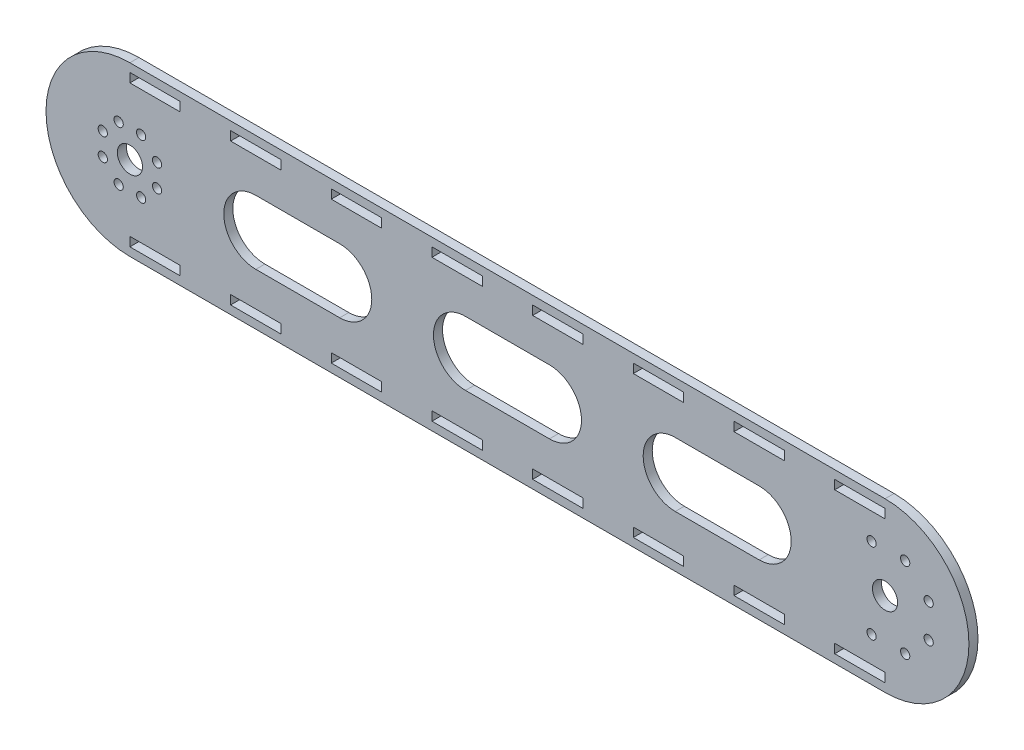
SolidWorks part; units mm, degrees
ref_plane "Front Plane" through (0, 0, 0) normal (0, 0, 1) x (1, 0, 0)
ref_plane "Top Plane" through (0, 0, 0) normal (0, 1, 0) x (1, 0, 0)
ref_plane "Right Plane" through (0, 0, 0) normal (1, 0, 0) x (0, 0, -1)
sketch "Sketch3" plane through (0, 0, 0) normal (0, 0, 1) x (1, 0, 0)
  line L0 (-20.9627, 0) -> (429.0373, 0) construction
  line L1 (-20.9627, 50) -> (429.0373, 50)
  line L2 (-20.9627, -50) -> (429.0373, -50)
  line L3 (179.0373, 0) -> (229.0373, 0) construction
  line L4 (179.0373, 19.0946) -> (229.0373, 19.0946)
  line L5 (179.0373, -19.0946) -> (229.0373, -19.0946)
  line L9 (-20.9627, 0) -> (-4.7949, 6.697)
  line L10 (-20.9627, 0) -> (-4.7949, 6.697) construction
  line L11 (-20.9627, 0) -> (-4.7949, -6.697) construction
  line L36 (-101.4371, 0) -> (436.7316, 0) construction
  line L64 (304.0053, 0) -> (354.0053, 0) construction
  line L65 (304.0053, 19.0946) -> (354.0053, 19.0946)
  line L66 (304.0053, -19.0946) -> (354.0053, -19.0946)
  line L67 (54.0693, 0) -> (104.0693, 0) construction
  line L68 (54.0693, 19.0946) -> (104.0693, 19.0946)
  line L69 (54.0693, -19.0946) -> (104.0693, -19.0946)
  line L99 (385.0007, 50) -> (385.0007, 44.46)
  arc A0 (-20.9627, 50) -> (-20.9627, -50) centre (-20.9627, 0) ccw
  arc A1 (429.0373, -50) -> (429.0373, 50) centre (429.0373, 0) ccw
  circle A2 centre (-20.9627, 0) radius 7.5
  circle A3 centre (429.0373, 0) radius 7.5
  arc A4 (179.0373, 19.0946) -> (179.0373, -19.0946) centre (179.0373, 0) ccw
  arc A5 (229.0373, -19.0946) -> (229.0373, 19.0946) centre (229.0373, 0) ccw
  circle A8 centre (-4.7949, 6.697) radius 2.75
  circle A9 centre (-4.7949, -6.697) radius 2.75
  circle A10 centre (-14.2658, -16.1679) radius 2.75
  circle A11 centre (-27.6597, -16.1679) radius 2.75
  circle A12 centre (-37.1306, -6.697) radius 2.75
  circle A13 centre (-37.1306, 6.697) radius 2.75
  circle A14 centre (-27.6597, 16.1679) radius 2.75
  circle A15 centre (-14.2658, 16.1679) radius 2.75
  circle A16 centre (455.0373, 10) radius 2.75
  circle A17 centre (441.0373, 24) radius 2.75
  circle A18 centre (421.0373, 24) radius 2.75
  circle A19 centre (455.0373, -10) radius 2.75
  circle A20 centre (441.0373, -24) radius 2.75
  circle A21 centre (421.0373, -24) radius 2.75
  arc A22 (304.0053, 19.0946) -> (304.0053, -19.0946) centre (304.0053, 0) ccw
  arc A23 (354.0053, -19.0946) -> (354.0053, 19.0946) centre (354.0053, 0) ccw
  arc A24 (54.0693, 19.0946) -> (54.0693, -19.0946) centre (54.0693, 0) ccw
  arc A25 (104.0693, -19.0946) -> (104.0693, 19.0946) centre (104.0693, 0) ccw
  point P3 (204.0373, 0)
  point P14 (204.0373, 0)
  point P59 (329.0053, 0)
  point P66 (79.0693, 0)
  dimension "D2" = 50
  dimension "D3" = 15
  dimension "D4" = 15
  dimension "D7" = 5.5
  dimension "D21" = 5.5
  dimension "D22" = 5.5
  dimension "D23" = 5.5
  dimension "D1" = 450
  dimension "D5" = 17.5
  dimension "D6" = 22.5
  dimension "D9" = 45
  dimension "D15" = 24
  dimension "D16" = 24
  dimension "D17" = 8
  dimension "D18" = 20
  dimension "D19" = 26
  dimension "D20" = 10
  dimension "D24" = 50
  dimension "D25" = 0
  dimension "D26" = 2
  dimension "D14" = 2
  dimension "D8" = 8
extrude "Boss-Extrude1" add sketch "Sketch3" along normal blind 5.4
sketch "Sketch4" plane through (0, 0, 5.4) normal (0, 0, 1) x (1, 0, 0)
  line L0 (-70.9627, 0) -> (479.0373, 0) construction
  line L1 (-20.9627, 50) -> (429.0373, 50) construction
  line L2 (-20.9627, 45) -> (9.0373, 45)
  line L3 (-20.9627, 45) -> (-20.9627, 39.6)
  line L4 (-20.9627, 39.6) -> (9.0373, 39.6)
  line L5 (9.0373, 45) -> (9.0373, 39.6)
  line L6 (39.0373, 45) -> (39.0373, 39.6)
  line L7 (39.0373, 45) -> (69.0373, 45)
  line L8 (69.0373, 45) -> (69.0373, 39.6)
  line L9 (39.0373, 39.6) -> (69.0373, 39.6)
  line L10 (99.0373, 45) -> (99.0373, 39.6)
  line L11 (99.0373, 45) -> (129.0373, 45)
  line L12 (129.0373, 45) -> (129.0373, 39.6)
  line L13 (99.0373, 39.6) -> (129.0373, 39.6)
  line L14 (159.0373, 45) -> (159.0373, 39.6)
  line L15 (159.0373, 45) -> (189.0373, 45)
  line L16 (189.0373, 45) -> (189.0373, 39.6)
  line L17 (159.0373, 39.6) -> (189.0373, 39.6)
  line L18 (219.0373, 45) -> (219.0373, 39.6)
  line L19 (219.0373, 45) -> (249.0373, 45)
  line L20 (249.0373, 45) -> (249.0373, 39.6)
  line L21 (219.0373, 39.6) -> (249.0373, 39.6)
  line L22 (279.0373, 45) -> (279.0373, 39.6)
  line L23 (279.0373, 45) -> (309.0373, 45)
  line L24 (309.0373, 45) -> (309.0373, 39.6)
  line L25 (279.0373, 39.6) -> (309.0373, 39.6)
  line L26 (339.0373, 45) -> (339.0373, 39.6)
  line L27 (339.0373, 45) -> (369.0373, 45)
  line L28 (369.0373, 45) -> (369.0373, 39.6)
  line L29 (339.0373, 39.6) -> (369.0373, 39.6)
  line L30 (399.0373, 45) -> (399.0373, 39.6)
  line L31 (399.0373, 45) -> (429.0373, 45)
  line L32 (429.0373, 45) -> (429.0373, 39.6)
  line L33 (399.0373, 39.6) -> (429.0373, 39.6)
  line L34 (399.0373, -45) -> (429.0373, -45)
  line L35 (429.0373, -45) -> (429.0373, -39.6)
  line L36 (399.0373, -39.6) -> (429.0373, -39.6)
  line L37 (399.0373, -45) -> (399.0373, -39.6)
  line L38 (339.0373, -45) -> (369.0373, -45)
  line L39 (369.0373, -45) -> (369.0373, -39.6)
  line L40 (339.0373, -39.6) -> (369.0373, -39.6)
  line L41 (339.0373, -45) -> (339.0373, -39.6)
  line L42 (279.0373, -45) -> (309.0373, -45)
  line L43 (309.0373, -45) -> (309.0373, -39.6)
  line L44 (279.0373, -39.6) -> (309.0373, -39.6)
  line L45 (279.0373, -45) -> (279.0373, -39.6)
  line L46 (219.0373, -45) -> (249.0373, -45)
  line L47 (249.0373, -45) -> (249.0373, -39.6)
  line L48 (219.0373, -39.6) -> (249.0373, -39.6)
  line L49 (219.0373, -45) -> (219.0373, -39.6)
  line L50 (159.0373, -45) -> (189.0373, -45)
  line L51 (189.0373, -45) -> (189.0373, -39.6)
  line L52 (159.0373, -39.6) -> (189.0373, -39.6)
  line L53 (159.0373, -45) -> (159.0373, -39.6)
  line L54 (99.0373, -45) -> (129.0373, -45)
  line L55 (129.0373, -45) -> (129.0373, -39.6)
  line L56 (99.0373, -39.6) -> (129.0373, -39.6)
  line L57 (99.0373, -45) -> (99.0373, -39.6)
  line L58 (39.0373, -45) -> (69.0373, -45)
  line L59 (69.0373, -45) -> (69.0373, -39.6)
  line L60 (39.0373, -39.6) -> (69.0373, -39.6)
  line L61 (39.0373, -45) -> (39.0373, -39.6)
  line L62 (-20.9627, -39.6) -> (9.0373, -39.6)
  line L63 (9.0373, -45) -> (9.0373, -39.6)
  line L64 (-20.9627, -45) -> (9.0373, -45)
  line L65 (-20.9627, -45) -> (-20.9627, -39.6)
  arc A0 (-20.9627, 50) -> (-20.9627, -50) centre (-20.9627, 0) ccw construction
  arc A1 (429.0373, -50) -> (429.0373, 50) centre (429.0373, 0) ccw construction
  dimension "D1" = 30
  dimension "D2" = 5.4
  dimension "D3" = 0
  dimension "D4" = 5
  dimension "D5" = 8
extrude "Cut-Extrude1" cut sketch "Sketch4" against normal through all
